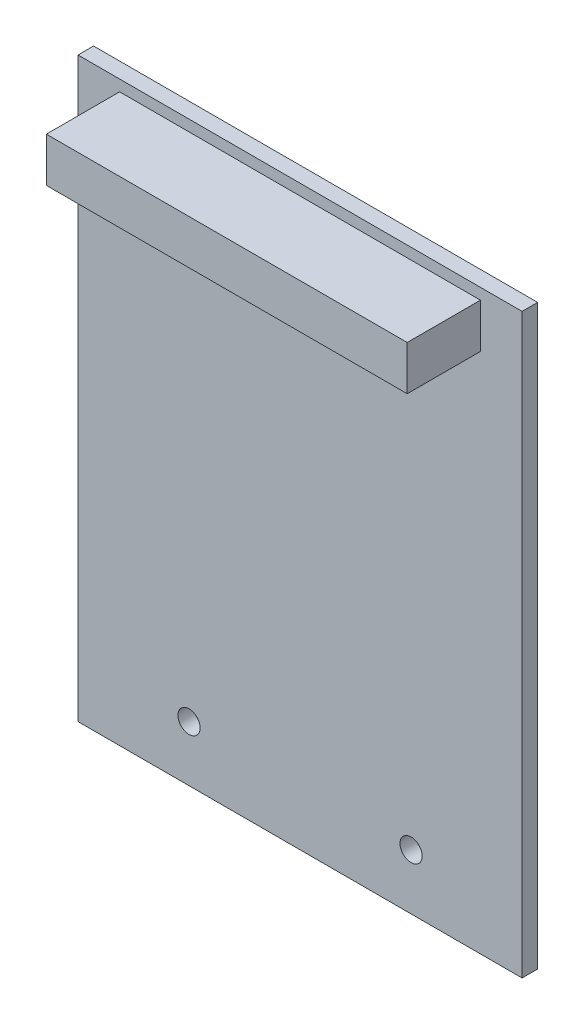
SolidWorks part; units mm, degrees
ref_plane "Front Plane" through (0, 0, 0) normal (0, 0, 1) x (1, 0, 0)
ref_plane "Top Plane" through (0, 0, 0) normal (0, 1, 0) x (1, 0, 0)
ref_plane "Right Plane" through (0, 0, 0) normal (1, 0, 0) x (0, 0, -1)
sketch "Sketch1" plane through (0, 0, 0) normal (0, 0, 1) x (1, 0, 0)
  line L1 (0, 66.04) -> (50.8, 66.04)
  line L2 (0, 66.04) -> (0, 0)
  line L3 (0, 0) -> (50.8, 0)
  line L4 (50.8, 66.04) -> (50.8, 0)
  dimension "D1" = 50.8
  dimension "D2" = 66.04
extrude "Boss-Extrude1" add sketch "Sketch1" along normal blind 1.778
sketch "Sketch2" plane through (0, 0, 1.778) normal (0, 0, 1) x (1, 0, 0)
  line L0 (25.4, 66.04) -> (25.4, 64.77) construction
  line L1 (4.7625, 64.77) -> (46.0375, 64.77)
  line L2 (4.7625, 64.77) -> (4.7625, 59.69)
  line L3 (4.7625, 59.69) -> (46.0375, 59.69)
  line L4 (46.0375, 64.77) -> (46.0375, 59.69)
  line L8 (50.8, 66.04) -> (0, 66.04) construction
  dimension "D1" = 5.08
  dimension "D2" = 41.275
  dimension "D3" = 1.27
extrude "Boss-Extrude2" add sketch "Sketch2" along normal blind 8.382
sketch "Sketch3" plane through (0, 0, 1.778) normal (0, 0, 1) x (1, 0, 0)
  line L0 (12.7, 6.35) -> (38.1, 6.35) construction
  line L1 (25.4, 6.35) -> (25.4, 0) construction
  line L3 (0, 0) -> (50.8, 0) construction
  circle A0 centre (12.7, 6.35) radius 1.27
  circle A1 centre (38.1, 6.35) radius 1.27
  dimension "D3" = 2.54
  dimension "D1" = 6.35
  dimension "D2" = 25.4
extrude "Cut-Extrude1" cut sketch "Sketch3" against normal up to surface (1.778 mm away) up to face at (25.4, 33.02, 0)
